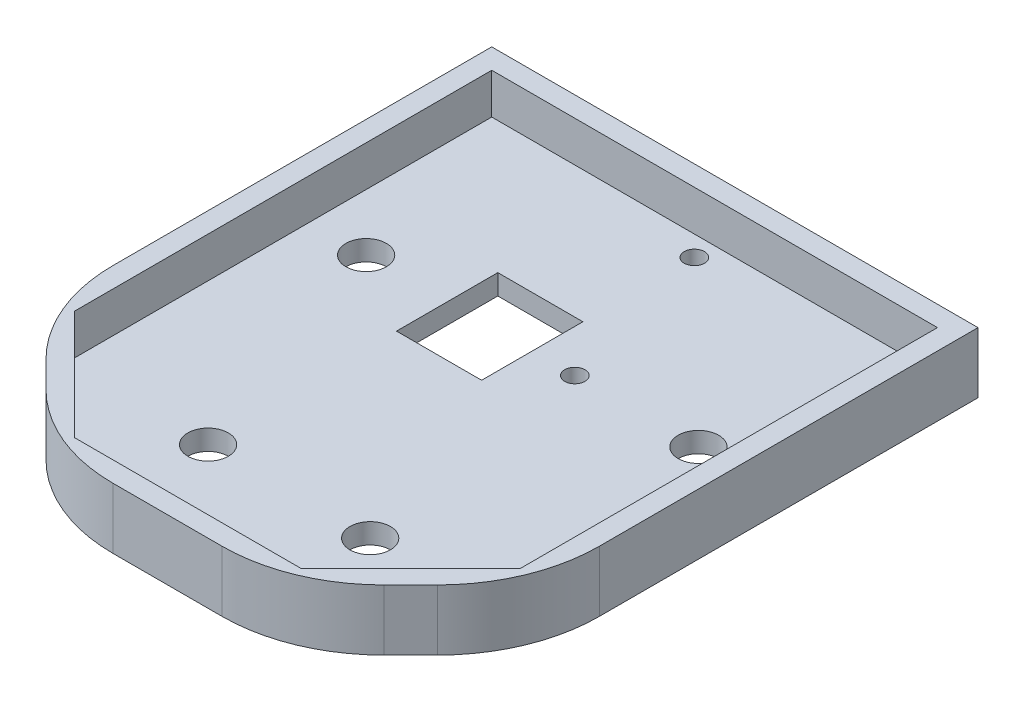
SolidWorks part; units mm, degrees
material "ABS"
ref_plane "Front Plane" through (0, 0, 0) normal (0, 0, 1) x (1, 0, 0)
ref_plane "Top Plane" through (0, 0, 0) normal (0, 1, 0) x (1, 0, 0)
ref_plane "Right Plane" through (0, 0, 0) normal (1, 0, 0) x (0, 0, -1)
sketch "Sketch1" plane through (0, 0, 0) normal (0, 1, 0) x (1, 0, 0)
  line L0 (-25.4, -50.8) -> (25.4, -50.8) construction
  line L1 (-76.2, 88.9) -> (76.2, 88.9)
  line L3 (-38.1, -88.9) -> (38.1, -88.9)
  line L4 (76.2, 88.9) -> (76.2, -50.8)
  line L5 (-76.2, 88.9) -> (76.2, -88.9) construction
  line L6 (-76.2, -88.9) -> (76.2, 88.9) construction
  line L7 (0, 88.9) -> (0, -88.9) construction
  line L8 (-52.07, 25.4) -> (52.07, 25.4) construction
  line L10 (-76.2, 88.9) -> (-76.2, -50.8)
  line L11 (-76.2, -50.8) -> (-38.1, -88.9)
  line L12 (38.1, -88.9) -> (76.2, -50.8)
  line L14 (-26.67, 9.525) -> (0, 9.525)
  line L15 (-26.67, 9.525) -> (-26.67, 41.275)
  line L16 (-26.67, 41.275) -> (0, 41.275)
  line L17 (0, 9.525) -> (0, 41.275)
  line L18 (-26.67, 9.525) -> (0, 41.275) construction
  line L19 (-26.67, 41.275) -> (0, 9.525) construction
  circle A1 centre (52.07, 25.4) radius 6.35
  circle A2 centre (-25.4, -50.8) radius 6.35
  circle A4 centre (25.4, -50.8) radius 6.35
  circle A9 centre (0, -76.2) radius 3.175
  circle A10 centre (0, 76.2) radius 3.175
  circle A12 centre (-52.07, 25.4) radius 6.35
  circle A13 centre (-52.07, 25.4) radius 25.4 construction
  circle A14 centre (-13.335, 25.4) radius 13.335 construction
  circle A15 centre (13.335, 25.4) radius 13.335 construction
  circle A16 centre (52.07, 25.4) radius 25.4 construction
  circle A17 centre (13.335, 25.4) radius 3.175
  point P0 (0, 0)
  point P16 (0, -50.8)
  point P17 (0, 25.4)
  dimension "D3" = 50.8
  dimension "D5" = 12.7
  dimension "D8" = 38.1
  dimension "D4" = 6.35
  dimension "D12" = 50.8
  dimension "D15" = 26.67
  dimension "D1" = 152.4
  dimension "D2" = 177.8
  dimension "D6" = 76.2
  dimension "D7" = 50.8
  dimension "D9" = 104.14
  dimension "D10" = 12.7
  dimension "D11" = 12.7
  dimension "D16" = 31.75
extrude "Boss-Extrude1" add sketch "Sketch1" along normal blind 6.35
sketch "Sketch2" plane through (0, 0, 0) normal (0, 1, 0) x (1, 0, 0)
  line L0 (-69.85, 82.55) -> (-69.85, -48.1697)
  line L1 (-69.85, -48.1697) -> (-35.4697, -82.55)
  line L2 (-35.4697, -82.55) -> (35.4697, -82.55)
  line L3 (35.4697, -82.55) -> (69.85, -48.1697)
  line L4 (69.85, -48.1697) -> (69.85, 82.55)
  line L5 (69.85, 82.55) -> (-69.85, 82.55)
  line L6 (-76.2, 88.9) -> (-76.2, -50.8)
  line L7 (-76.2, -50.8) -> (-38.1, -88.9)
  line L8 (-38.1, -88.9) -> (38.1, -88.9)
  line L9 (38.1, -88.9) -> (76.2, -50.8)
  line L10 (76.2, -50.8) -> (76.2, 88.9)
  line L11 (76.2, 88.9) -> (-76.2, 88.9)
  line L12 (-76.2, 88.9) -> (-76.2, -50.8)
  line L13 (-76.2, -50.8) -> (-38.1, -88.9)
  line L14 (-38.1, -88.9) -> (38.1, -88.9)
  line L15 (38.1, -88.9) -> (76.2, -50.8)
  line L16 (76.2, -50.8) -> (76.2, 88.9)
  line L17 (76.2, 88.9) -> (-76.2, 88.9)
  dimension "D1" = 0
  dimension "D2" = 6.35
extrude "Boss-Extrude2" add sketch "Sketch2" along normal blind 19.05
fillet "Fillet1" radius 50.8 4 edges at (76.2, 9.525, 50.8) (38.1, 9.525, 88.9) (-38.1, 9.525, 88.9) (-76.2, 9.525, 50.8)
